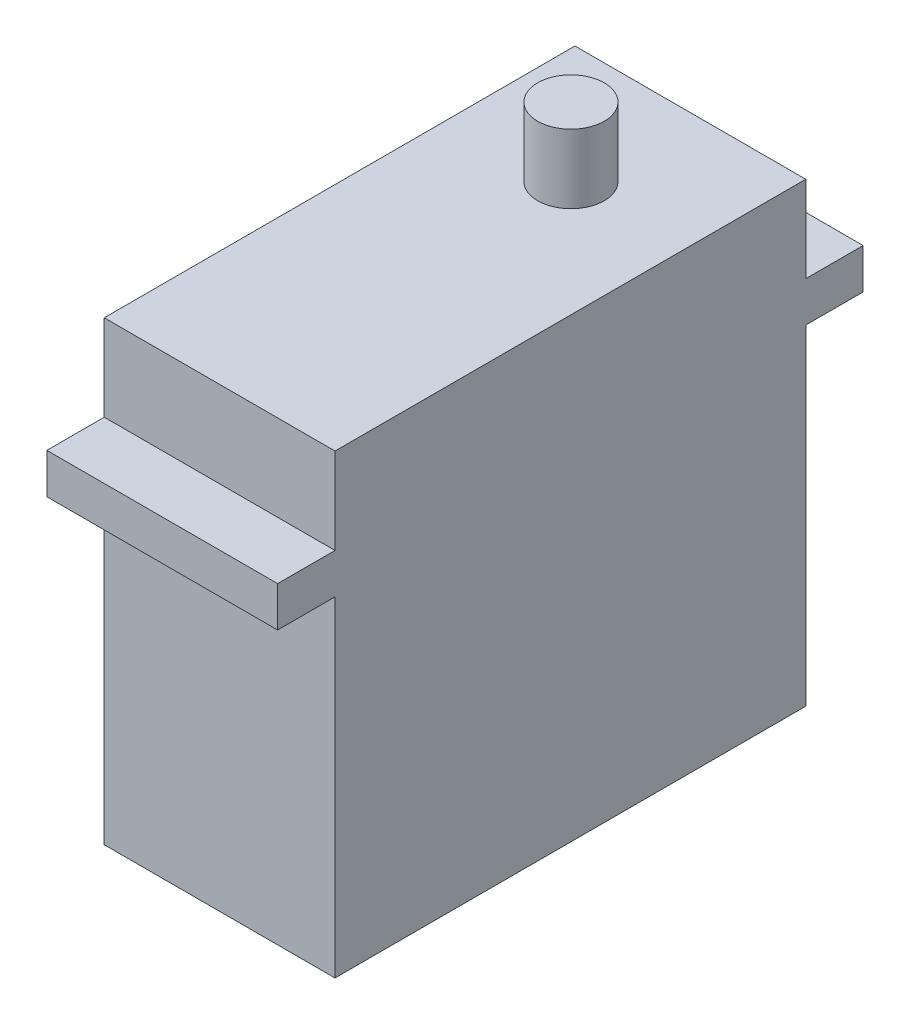
SolidWorks part; units mm, degrees
ref_plane "Front Plane" through (0, 0, 0) normal (0, 0, 1) x (1, 0, 0)
ref_plane "Top Plane" through (0, 0, 0) normal (0, 1, 0) x (1, 0, 0)
ref_plane "Right Plane" through (0, 0, 0) normal (1, 0, 0) x (0, 0, -1)
sketch "Sketch2" plane through (0, 0, 0) normal (1, 0, 0) x (0, 0, -1)
  line L1 (-20.5, 19.875) -> (20.5, 19.875)
  line L2 (-20.5, 19.875) -> (-20.5, -19.875)
  line L3 (-20.5, -19.875) -> (20.5, -19.875)
  line L4 (20.5, 19.875) -> (20.5, -19.875)
  line L5 (-20.5, 19.875) -> (20.5, -19.875) construction
  line L6 (-20.5, -19.875) -> (20.5, 19.875) construction
  line L7 (20.5, 12.375) -> (25.5, 12.375)
  line L8 (20.5, 12.375) -> (20.5, 8.875)
  line L9 (20.5, 8.875) -> (25.5, 8.875)
  line L10 (25.5, 12.375) -> (25.5, 8.875)
  line L11 (-20.5, 12.375) -> (-25.5, 12.375)
  line L12 (-20.5, 12.375) -> (-20.5, 8.875)
  line L13 (-20.5, 8.875) -> (-25.5, 8.875)
  line L14 (-25.5, 12.375) -> (-25.5, 8.875)
  line L16 (-25.5, 10.625) -> (25.5, 10.625) construction
  line L17 (7.2, 19.875) -> (13, 19.875)
  line L18 (7.2, 19.875) -> (7.2, 25.875)
  line L19 (7.2, 25.875) -> (13, 25.875)
  line L20 (13, 19.875) -> (13, 25.875)
  point P0 (0, 0)
  point P22 (0, 10.625)
  dimension "D1" = 32.25
  dimension "D2" = 41
  dimension "D3" = 45.75
  dimension "D4" = 51
  dimension "D5" = 39.75
  dimension "D6" = 3.5
  dimension "D7" = 5.8
  dimension "D8" = 7.5
extrude "Boss-Extrude1" add sketch "Sketch2" along normal blind 20.1 contours L4 L1 L2 L3 | L11 L14 L13 L2 | L1 L20 L19 L18 | L10 L7 L4 L9
sketch "Sketch3" plane through (0, 19.875, 0) normal (0, 1, 0) x (1, 0, 0)
  line L0 (20.1, 13) -> (0, 13) construction
  line L1 (20.1, 7.2) -> (12.95, 7.2)
  line L2 (20.1, 7.2) -> (20.1, 13)
  line L3 (20.1, 13) -> (12.95, 13)
  line L4 (12.95, 7.2) -> (12.95, 13)
  line L5 (20.1, 13) -> (0, 13) construction
  line L6 (0, 7.2) -> (7.15, 7.2)
  line L7 (0, 7.2) -> (0, 13)
  line L8 (0, 13) -> (7.15, 13)
  line L9 (7.15, 7.2) -> (7.15, 13)
  line L10 (20.1, 25.5) -> (0, 25.5) construction
  line L11 (12.95, 13) -> (7.15, 13)
  line L12 (12.95, 7.2) -> (7.15, 7.2)
  circle A0 centre (10.05, 10.1) radius 2.9
  point P15 (7.15, 10.1)
  point P21 (10.05, 25.5)
  line M7 (20.1, 7.2) -> (0, 7.2)
extrude "Cut-Extrude1" cut sketch "Sketch3" along normal up to surface (6 mm away) contours A0 L4 M7 | A0 L4 L11 | A0 L11 L9 | A0 L9 L12 | L9 L8 L7 M7 | L4 L2 L3 M7 up to face at (10.05, 25.875, -10.1)
